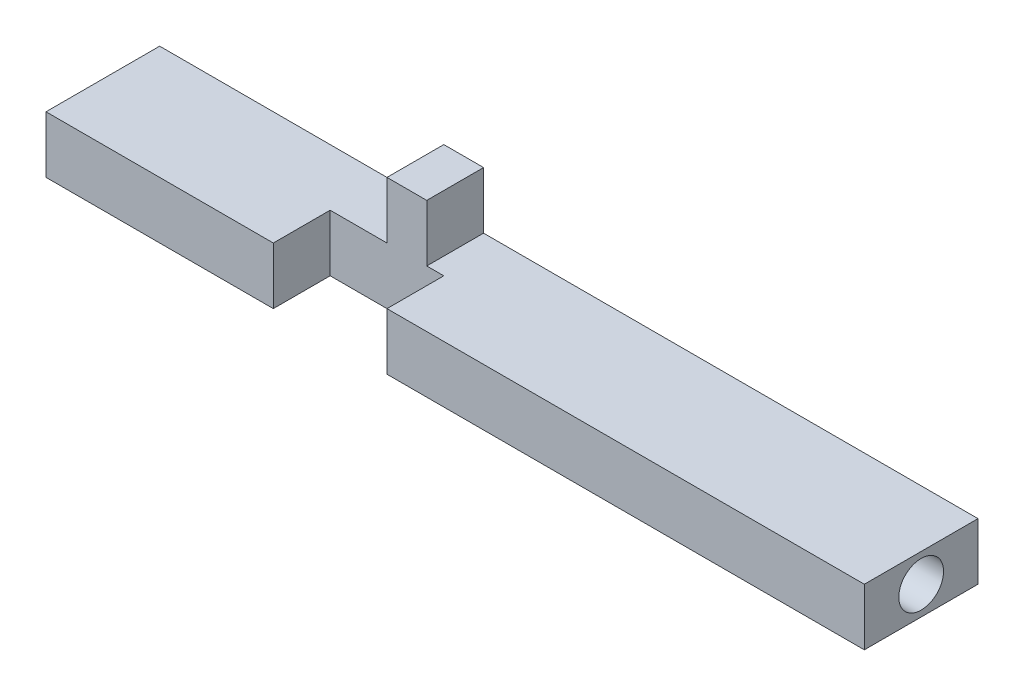
SolidWorks part; units mm, degrees
material "Polylactic Acid (PLA)"
ref_plane "Front Plane" through (0, 0, 0) normal (0, 0, 1) x (1, 0, 0)
ref_plane "Top Plane" through (0, 0, 0) normal (0, 1, 0) x (1, 0, 0)
ref_plane "Right Plane" through (0, 0, 0) normal (1, 0, 0) x (0, 0, -1)
sketch "Sketch1" plane through (0, 0, 0) normal (0, 1, 0) x (1, 0, 0)
  line L0 (0, -3.175) -> (0, 3.175) construction
  line L1 (-22.86, -3.175) -> (22.86, -3.175)
  line L2 (-22.86, -3.175) -> (-22.86, 3.175)
  line L3 (-22.86, 3.175) -> (22.86, 3.175)
  line L4 (22.86, -3.175) -> (22.86, 3.175)
  line L5 (-22.86, -3.175) -> (22.86, 3.175) construction
  line L6 (-22.86, 3.175) -> (22.86, -3.175) construction
  point P0 (0, 0)
  point P9 (0, 0)
  dimension "D1" = 45.72
  dimension "D2" = 6.35
extrude "Boss-Extrude1" add sketch "Sketch1" along normal mid plane 3.175
sketch "Sketch3" plane through (-22.86, 0, 0) normal (-1, 0, 0) x (0, 0, 1)
  circle A0 centre (0, 0) radius 1.25
  dimension "D1" = 2.5
sketch "Sketch4" plane through (0, 0, 3.175) normal (0, 0, 1) x (1, 0, 0)
  line L6 (-10.16, -1.5875) -> (-3.81, -1.5875)
  line L10 (-10.16, -1.5875) -> (-10.16, 1.5875)
  line L11 (-10.16, 1.5875) -> (-3.81, 1.5875)
  line L12 (-3.81, -1.5875) -> (-3.81, 1.5875)
  line L13 (-10.16, -1.5875) -> (-3.81, 1.5875) construction
  line L14 (-10.16, 1.5875) -> (-3.81, -1.5875) construction
  point P0 (-6.985, 0)
  dimension "D1" = 3.81
  dimension "D2" = 6.35
  dimension "D3" = 3.175
  dimension "D4" = 0
extrude "Cut-Extrude1" cut sketch "Sketch4" against normal blind 3.175
sketch "Sketch5" plane through (0, 1.5875, 0) normal (0, 1, 0) x (1, 0, 0)
  line L9 (-6.985, 0) -> (-6.985, 3.175)
  line L10 (-3.81, 0) -> (-10.16, 0) construction
  line L11 (22.86, 3.175) -> (-22.86, 3.175) construction
  line L12 (-6.985, 0) -> (-4.7625, 0)
  line L13 (-4.7625, 0) -> (-4.7625, 3.175)
  line L14 (-4.7625, 3.175) -> (-6.985, 3.175)
  dimension "D1" = 2.2225
extrude "Boss-Extrude3" add sketch "Sketch5" along normal blind 3.175
extrude "Cut-Extrude2" cut sketch "Sketch3" against normal blind 6.985
mirror "Mirror1" about plane through (0, 0, 0) normal (1, 0, 0) of "Cut-Extrude2"
